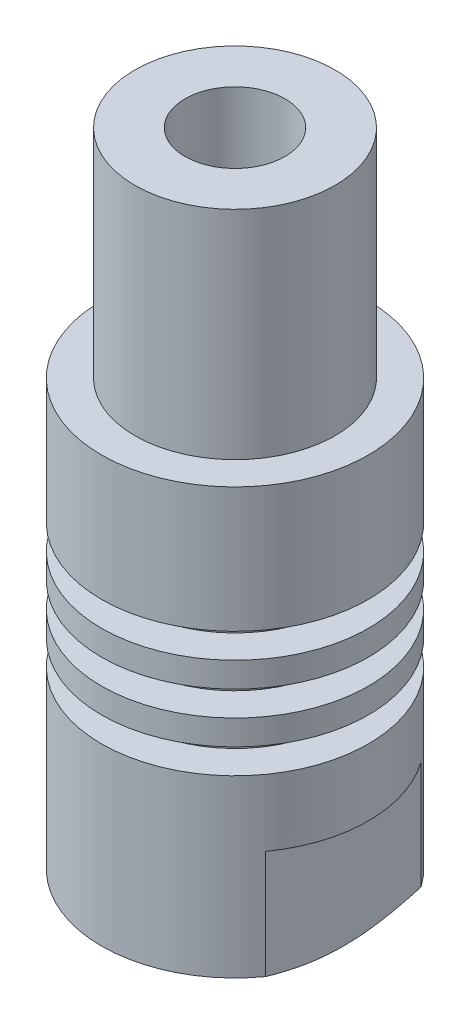
SolidWorks part; units mm, degrees
material "Gomma"
ref_plane "Piano frontale" through (0, 0, 0) normal (0, 0, 1) x (1, 0, 0)
ref_plane "Piano superiore" through (0, 0, 0) normal (0, 1, 0) x (1, 0, 0)
ref_plane "Piano destro" through (0, 0, 0) normal (1, 0, 0) x (0, 0, -1)
sketch "Schizzo1" plane through (0, 0, 0) normal (0, 0, 1) x (1, 0, 0)
  line L0 (0, 0) -> (-5, 0)
  line L1 (-5, 0) -> (-8, 1.5)
  line L2 (-8, 1.5) -> (-8, 12)
  line L3 (-8, 12) -> (-6, 12)
  line L4 (-6, 12) -> (-6, 13.5)
  line L5 (-6, 13.5) -> (-8, 13.5)
  line L6 (-8, 13.5) -> (-8, 15)
  line L7 (-8, 15) -> (-6, 15)
  line L8 (-6, 15) -> (-6, 16.5)
  line L9 (-6, 16.5) -> (-8, 16.5)
  line L10 (-8, 16.5) -> (-8, 18)
  line L11 (-8, 18) -> (-6, 18)
  line L12 (-6, 18) -> (-6, 19.5)
  line L13 (-6, 19.5) -> (-8, 19.5)
  line L14 (-8, 19.5) -> (-8, 27)
  line L15 (-8, 40) -> (0, 40)
  line L18 (-8, 27) -> (-8, 40)
  line L20 (0, 40) -> (0, 0)
  line L21 (0, 129.4074) -> (0, -17.2322) construction
  dimension "D1" = 1.5
  dimension "D2" = 16
  dimension "D3" = 2
  dimension "D4" = 40
  dimension "D5" = 12
  dimension "D8" = 1.5
  dimension "D10" = 10
  dimension "D11" = 12
  dimension "D12" = 1.5
  dimension "D13" = 1.5
revolve "Rivoluzione1" add sketch "Schizzo1" angle 360 about L21
sketch "Schizzo2" plane through (0, 0, 0) normal (0, 0, 1) x (1, 0, 0)
  line L0 (-8, 8) -> (-6.5, 8)
  line L1 (-6.5, 8) -> (-6.5, 0)
  line L2 (-6.5, 0) -> (-8, 0)
  line L3 (-8, 0) -> (-8, 8)
  line L4 (6.5, 8) -> (6.5, 0)
  line L5 (6.5, 0) -> (8, 0)
  line L6 (8, 0) -> (8, 8)
  line L7 (8, 8) -> (6.5, 8)
  line L8 (0, 0) -> (0, 9.0399) construction
  line L9 (-5, 0) -> (5, 0) construction
  line L11 (8, 1.5) -> (8, 12) construction
  line L12 (-8, 12) -> (-8, 1.5) construction
  dimension "D2" = 1.5
extrude "Taglio-Estrusione1" cut sketch "Schizzo2" against normal up to next and the other way up to next
sketch "Schizzo7" plane through (0, 40, 0) normal (0, 1, 0) x (1, 0, 0)
  circle A0 centre (0, 0) radius 3
extrude "Taglio-Estrusione2" cut sketch "Schizzo7" against normal through all
hole_wizard "Foro filettato M8-1" positions "Schizzo9" profile "Schizzo8" tap size "M8" standard "ISO"
sketch "Schizzo9" plane through (0, 0, 0) normal (0, -1, 0) x (-1, 0, 0)
  point P0 (0, 0)
sketch "Schizzo8" plane through (0, 0, 0) normal (1, 0, 0) x (0, 0, -1)
  line L0 (0, 0) -> (0, 14.0429)
  line L1 (0, 14.0429) -> (3.4, 12)
  line L2 (3.4, 12) -> (3.4, 0)
  line L5 (3.4, 0) -> (0, 0)
  line L10 (0, 14.0429) -> (-3.4, 12) construction
  line L11 (0, -6.35) -> (0, 107.95) construction
  dimension "Tap Drill Dia." = 6.8
  dimension "Tap Drill Depth" = 12
  dimension "Drill Angle" = 118
cosmetic thread "Filettatura del foro3" parameters "D1"=12, "D2"=8
sketch "Schizzo10" plane through (0, 40, 0) normal (0, 1, 0) x (1, 0, 0)
  circle A0 centre (0, 0) radius 6
  dimension "D1" = 12
extrude "Taglio-Estrusione3" cut sketch "Schizzo10" against normal blind 13 flip side to cut
